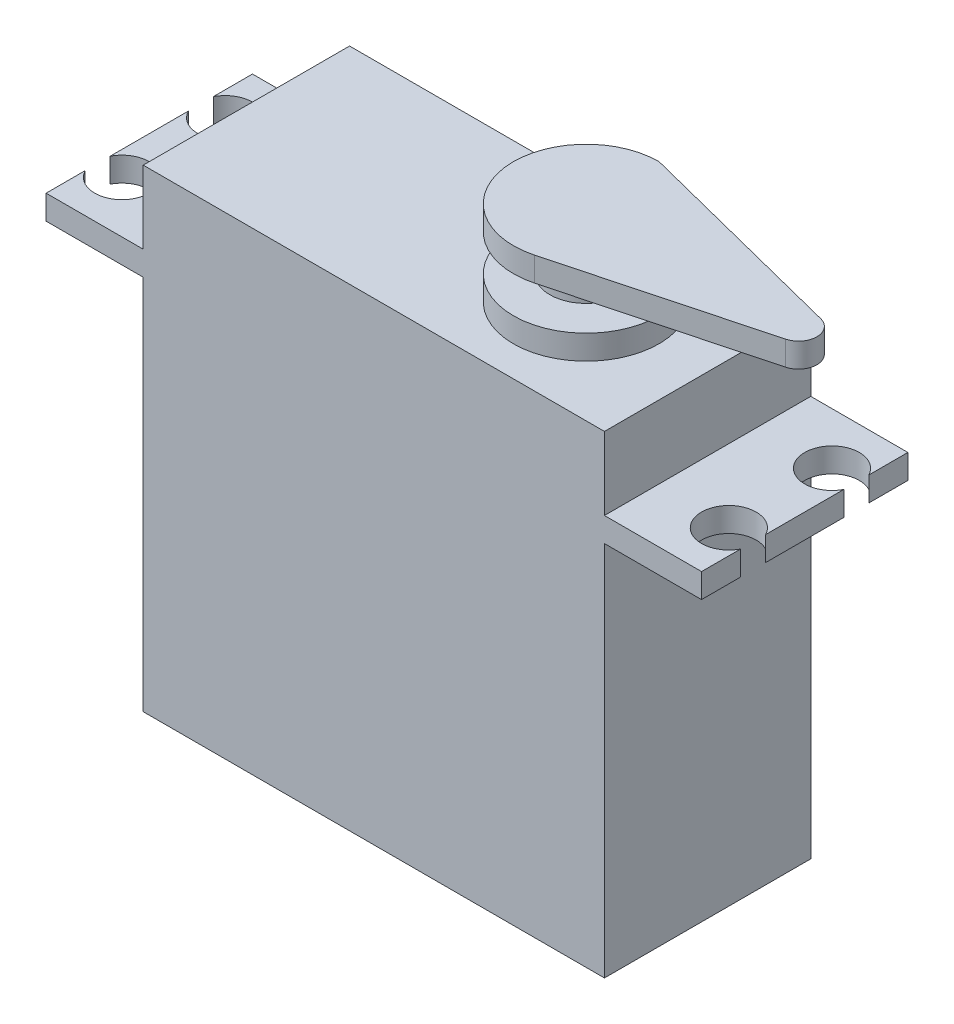
SolidWorks part; units mm, degrees
ref_plane "Front Plane" through (0, 0, 0) normal (0, 0, 1) x (1, 0, 0)
ref_plane "Top Plane" through (0, 0, 0) normal (0, 1, 0) x (1, 0, 0)
ref_plane "Right Plane" through (0, 0, 0) normal (1, 0, 0) x (0, 0, -1)
sketch "Sketch1" plane through (0, 0, 0) normal (0, 1, 0) x (1, 0, 0)
  line L0 (-24.7214, 0) -> (37.6329, 0) construction
  line L1 (-19, 8.5) -> (19, 8.5)
  line L2 (-19, 8.5) -> (-19, -8.5)
  line L3 (-19, -8.5) -> (19, -8.5)
  line L4 (19, 8.5) -> (19, -8.5)
  line L5 (0, 14.4106) -> (0, -20.285) construction
  dimension "D1" = 38
  dimension "D2" = 17
extrude "Boss-Extrude1" add sketch "Sketch1" along normal blind 39
ref_plane "Plane1" through (0, 31, 0) normal (0, 1, 0) x (1, 0, 0)
sketch "Sketch2" plane through (0, 31, 0) normal (0, 1, 0) x (1, 0, 0)
  line L0 (42.0173, 4.25) -> (-30.3034, 4.25) construction
  line L1 (19, 8.5) -> (27, 8.5)
  line L2 (19, 8.5) -> (19, -8.5)
  line L3 (19, -8.5) -> (27, -8.5)
  line L4 (27, 8.5) -> (27, 5.2808)
  line L5 (19, -8.5) -> (19, 8.5) construction
  line L6 (19, 8.5) -> (-19, 8.5) construction
  line L7 (-19, -8.5) -> (19, -8.5) construction
  line L8 (-25.0835, 0) -> (45.5521, 0) construction
  line L9 (27, 3.2192) -> (27, -3.2192)
  line L10 (27, -5.2808) -> (27, -8.5)
  arc A0 (27, 5.2808) -> (27, 3.2192) centre (25, 4.25) ccw
  arc A1 (27, -5.2808) -> (27, -3.2192) centre (25, -4.25) cw
  dimension "D2" = 4.5
  dimension "D1" = 8
  dimension "D3" = 25
  dimension "D4" = 4.25
extrude "Boss-Extrude2" add sketch "Sketch2" along normal blind 2
mirror "Mirror1" about plane through (0, 0, 0) normal (1, 0, 0) of "Boss-Extrude2"
sketch "Sketch3" plane through (0, 39, 0) normal (0, 1, 0) x (1, 0, 0)
  line L0 (0, 0) -> (32.2442, 0) construction
  line L1 (19, -8.5) -> (19, 8.5) construction
  circle A0 centre (9, 0) radius 6
  point P2 (0, 0)
  dimension "D1" = 12
  dimension "D2" = 10
extrude "Boss-Extrude3" add sketch "Sketch3" along normal blind 2
sketch "Sketch4" plane through (0, 41, 0) normal (0, 1, 0) x (1, 0, 0)
  circle A0 centre (9, 0) radius 3
  circle A1 centre (9, 0) radius 6 construction
  dimension "D1" = 6
extrude "Boss-Extrude4" add sketch "Sketch4" along normal blind 3
sketch "Sketch5" plane through (0, 44, 0) normal (0, 1, 0) x (1, 0, 0)
  line L0 (9, 6) -> (26.8698, 1.4537)
  line L1 (9, 0) -> (38.6786, 0) construction
  line L2 (10.5429, -5.7982) -> (26.8857, -1.4496)
  arc A0 (9, 6) -> (10.5429, -5.7982) centre (9, 0) ccw
  arc A1 (26.8857, -1.4496) -> (26.8698, 1.4537) centre (26.5, 0) ccw
  circle A2 centre (9, 0) radius 6 construction
  point P7 (32.5907, -2.8557)
  point P8 (10.0492, -4.7716)
  point P11 (11.0252, -4.0848)
  point P14 (31.7044, -2.205)
  point P15 (0, 0)
  point P16 (9.3639, -5.989)
  dimension "D2" = 3
  dimension "D1" = 19
extrude "Boss-Extrude5" add sketch "Sketch5" along normal blind 2
